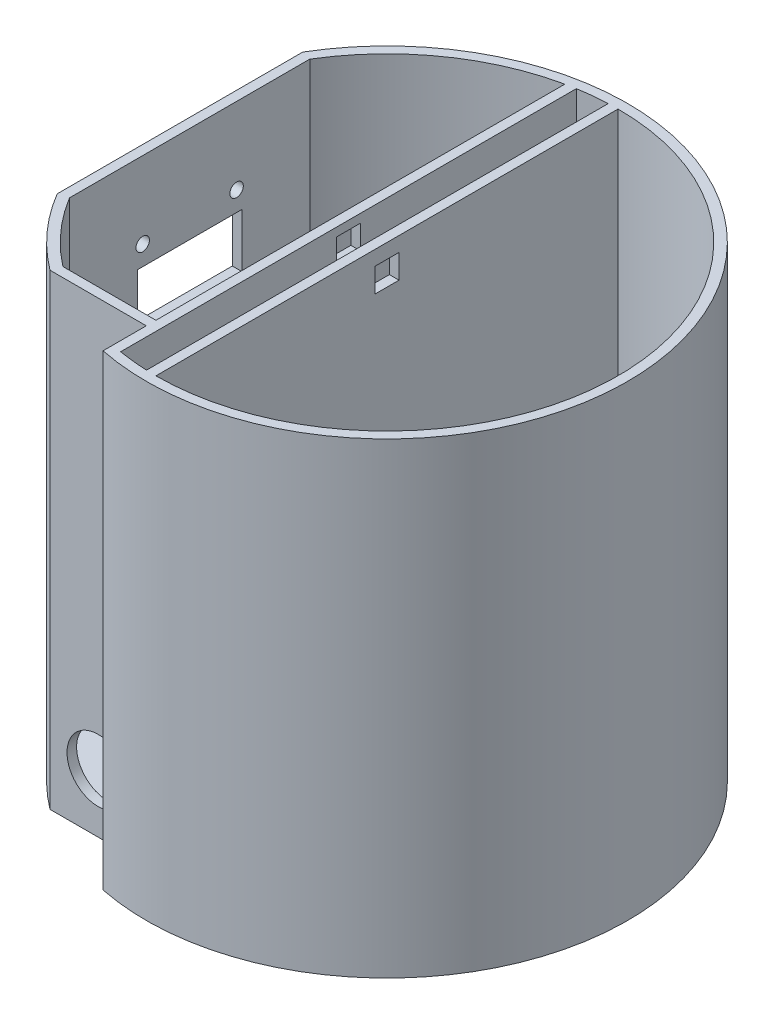
SolidWorks part; units mm, degrees
ref_plane "Front Plane" through (0, 0, 0) normal (0, 0, 1) x (1, 0, 0)
ref_plane "Top Plane" through (0, 0, 0) normal (0, 1, 0) x (1, 0, 0)
ref_plane "Right Plane" through (0, 0, 0) normal (1, 0, 0) x (0, 0, -1)
sketch "Sketch2" plane through (0, 0, 0) normal (0, 1, 0) x (1, 0, 0)
  line L0 (-43, 25.5147) -> (-43, -25.5147)
  line L1 (-30, -40) -> (-10, -40)
  line L2 (-10, -40) -> (-10, -48.9898)
  arc A0 (-43, -25.5147) -> (-30, -40) centre (0, 0) ccw
  arc A1 (-10, -48.9898) -> (-43, 25.5147) centre (0, 0) ccw
  dimension "D1" = 100
  dimension "D2" = 43
  dimension "D3" = 40
  dimension "D4" = 10
extrude "Boss-Extrude1" add sketch "Sketch2" along normal blind 3
sketch "Sketch3" plane through (0, 3, 0) normal (0, 1, 0) x (1, 0, 0)
  line L0 (-43, 25.5147) -> (-43, -25.5147)
  line L1 (-30, -40) -> (-10, -40)
  line L2 (-10, -40) -> (-10, -48.9898)
  line L3 (-41, 24.96) -> (-41, -24.96)
  line L4 (-29.3258, -38) -> (-10, -38)
  line L5 (-8, -38) -> (-8, -47.3286)
  line L6 (-8, -38) -> (-8, 47.3286)
  line L7 (-10, -38) -> (-10, 46.9468)
  line L8 (0, 0) -> (0, 48)
  line L9 (0, 0) -> (0, -48)
  line L10 (-2, 47.9583) -> (-2, -47.9583)
  arc A0 (-43, -25.5147) -> (-30, -40) centre (0, 0) ccw
  arc A1 (-41, -24.96) -> (-29.3258, -38) centre (0, 0) ccw
  arc A2 (-10, -48.9898) -> (-43, 25.5147) centre (0, 0) ccw
  arc A3 (-8, -47.3286) -> (-2, -47.9583) centre (0, 0) ccw
  arc A4 (-10, 46.9468) -> (-41, 24.96) centre (0, 0) ccw
  arc A5 (-2, 47.9583) -> (-8, 47.3286) centre (0, 0) ccw
  arc A6 (0, -48) -> (0, 48) centre (0, 0) ccw
  dimension "D1" = 96
  dimension "D2" = 100
  dimension "D3" = 2
  dimension "D4" = 2
  dimension "D5" = 2
extrude "Boss-Extrude2" add sketch "Sketch3" along normal blind 94
sketch "Sketch4" plane through (-43, 0, 0) normal (-1, 0, 0) x (0, 0, 1)
  line L0 (0, 128.2198) -> (0, -29.2286) construction
  line L1 (0, 65.82) -> (10.87, 65.82)
  line L2 (10.87, 65.82) -> (10.87, 77)
  line L3 (10.87, 77) -> (-10.87, 77)
  line L4 (-10.87, 77) -> (-10.87, 65.82)
  line L5 (-10.87, 65.82) -> (0, 65.82)
  line L6 (-25.5147, 97) -> (25.5147, 97) construction
  line L7 (-25.5147, 106.808) -> (25.5147, 106.808) construction
  line L8 (-7.5, 55.5907) -> (7.5, 55.5907)
  line L9 (7.5, 55.5907) -> (7.5, 51.5907)
  line L10 (7.5, 51.5907) -> (0, 51.5907)
  line L11 (0, 51.5907) -> (-7.5, 51.5907)
  line L12 (-7.5, 51.5907) -> (-7.5, 55.5907)
  line L13 (0, 35.0689) -> (6, 35.0689)
  line L14 (6, 35.0689) -> (6, 19.5689)
  line L15 (6, 19.5689) -> (-6, 19.5689)
  line L16 (-6, 19.5689) -> (-6, 35.0689)
  line L17 (-6, 35.0689) -> (0, 35.0689)
  line L18 (-20.267, 83.08) -> (25.5147, 83.08) construction
  line L19 (-14.3031, 81.08) -> (15.9664, 81.08) construction
  line L20 (-9.75, 86.9366) -> (-9.75, 75.2339) construction
  line L21 (-14.3031, 40.0689) -> (22.009, 40.0689) construction
  circle A0 centre (-9.75, 81.0853) radius 1.4
  circle A1 centre (9.75, 81.0853) radius 1.4
  circle A2 centre (0, 40.0689) radius 1.25
  dimension "D11" = 2.8
  dimension "D13" = 2.5
  dimension "D1" = 21.74
  dimension "D2" = 11.18
  dimension "D3" = 20
  dimension "D4" = 15
  dimension "D5" = 4
  dimension "D6" = 12
  dimension "D7" = 15.5
  dimension "D8" = 6.08
  dimension "D9" = 2
  dimension "D10" = 1.12
  dimension "D12" = 5
extrude "Cut-Extrude1" cut sketch "Sketch4" against normal blind 2
sketch "Sketch5" plane through (0, 0, 40) normal (0, 0, 1) x (1, 0, 0)
  line L0 (-54.7737, 12) -> (58.1124, 12) construction
  line L1 (-30, 0) -> (-10, 0) construction
  circle A0 centre (-19.9742, 12) radius 6.5
  dimension "D1" = 13
  dimension "D2" = 12
extrude "Cut-Extrude2" cut sketch "Sketch5" against normal blind 2
sketch "Sketch6" plane through (-10, 0, 0) normal (-1, 0, 0) x (0, 0, 1)
  line L0 (0, 0) -> (0, 101.5552) construction
  line L1 (-27.5, 82) -> (27.5, 82) construction
  line L2 (27.5, 82) -> (27.5, 9) construction
  line L3 (27.5, 9) -> (0, 9) construction
  line L4 (0, 9) -> (-27.5, 9) construction
  line L5 (-27.5, 9) -> (-27.5, 82) construction
  line L6 (-25.5147, 97) -> (25.5147, 97) construction
  line L7 (0, 88.8398) -> (15, 88.8398) construction
  line L8 (15, 88.8398) -> (15, 58.8398) construction
  line L9 (15, 58.8398) -> (-15, 58.8398) construction
  line L10 (-15, 58.8398) -> (-15, 88.8398) construction
  line L11 (-15, 88.8398) -> (0, 88.8398) construction
  line L12 (-2.5, 95.223) -> (0, 95.223)
  line L13 (0, 95.223) -> (2.5, 95.223)
  line L14 (2.5, 95.223) -> (2.5, 90.223)
  line L15 (2.5, 90.223) -> (-2.5, 90.223)
  line L16 (-2.5, 90.223) -> (-2.5, 95.223)
  circle A0 centre (-27.5, 82) radius 1
  circle A1 centre (27.5, 82) radius 1
  circle A2 centre (27.5, 9) radius 1
  circle A3 centre (-27.5, 9) radius 1
  circle A4 centre (-15, 88.8398) radius 1.25
  circle A5 centre (15, 88.8398) radius 1.25
  circle A6 centre (15, 58.8398) radius 1.25
  circle A7 centre (-15, 58.8398) radius 1.25
  dimension "D4" = 2
  dimension "D5" = 2
  dimension "D6" = 2
  dimension "D7" = 2
  dimension "D11" = 2.5
  dimension "D12" = 2.5
  dimension "D13" = 2.5
  dimension "D14" = 2.5
  dimension "D1" = 55
  dimension "D2" = 73
  dimension "D3" = 15
  dimension "D8" = 15
  dimension "D9" = 15
  dimension "D10" = 30
  dimension "D15" = 5
  dimension "D16" = 5
extrude "Cut-Extrude3" cut sketch "Sketch6" against normal blind 2
sketch "Sketch7" plane through (-2, 0, 0) normal (-1, 0, 0) x (0, 0, 1)
  line L0 (0, 0) -> (0, 99.2187) construction
  line L1 (-2.5, 93.9609) -> (0, 93.9609)
  line L2 (0, 93.9609) -> (2.5, 93.9609)
  line L3 (2.5, 93.9609) -> (2.5, 88.9609)
  line L4 (2.5, 88.9609) -> (-2.5, 88.9609)
  line L5 (-2.5, 88.9609) -> (-2.5, 93.9609)
  dimension "D1" = 2.5
  dimension "D2" = 2.5
  dimension "D3" = 5
extrude "Cut-Extrude4" cut sketch "Sketch7" against normal blind 2
